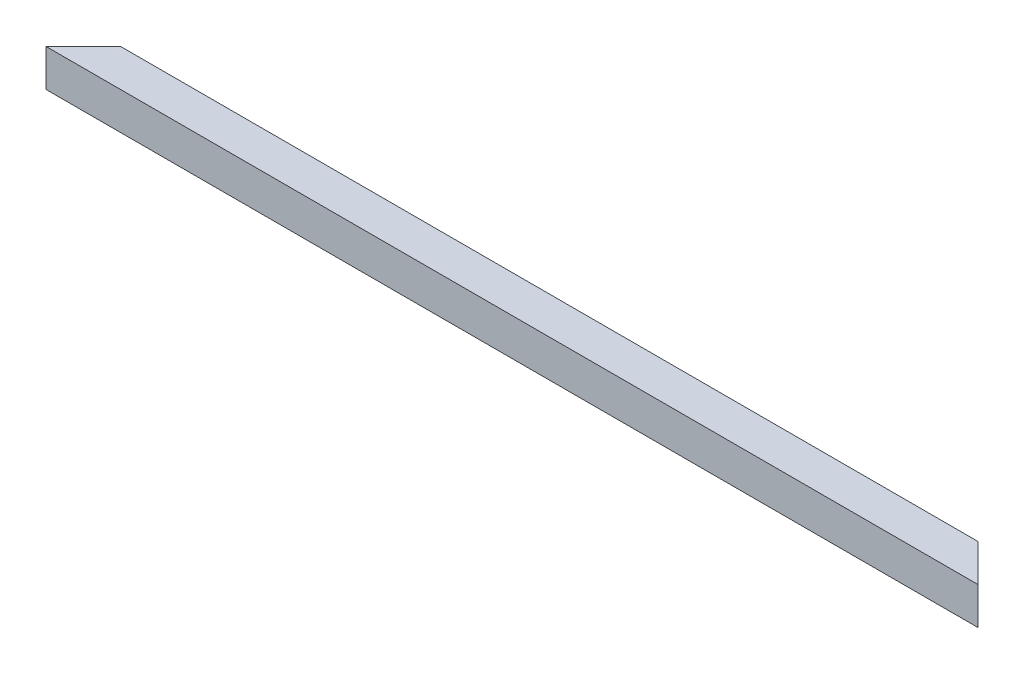
SolidWorks part; units mm, degrees
ref_plane "Alzado" through (0, 0, 0) normal (0, 0, 1) x (1, 0, 0)
ref_plane "Planta" through (0, 0, 0) normal (0, 1, 0) x (1, 0, 0)
ref_plane "Vista lateral" through (0, 0, 0) normal (1, 0, 0) x (0, 0, -1)
sketch "Croquis1" plane through (0, 0, 0) normal (1, 0, 0) x (0, 0, -1)
  line L1 (-20, -20) -> (20, -20)
  line L2 (-20, -20) -> (-20, 20)
  line L3 (-20, 20) -> (20, 20)
  line L4 (20, -20) -> (20, 20)
  line L5 (-20, -20) -> (20, 20) construction
  line L6 (-20, 20) -> (20, -20) construction
  line L7 (18, -18) -> (-18, -18)
  line L8 (18, -18) -> (18, 18)
  line L9 (18, 18) -> (-18, 18)
  line L10 (-18, -18) -> (-18, 18)
  line L11 (18, -18) -> (-18, 18) construction
  line L12 (18, 18) -> (-18, -18) construction
  point P0 (0, 0)
  point P6 (0, 0)
  dimension "D1" = 40
  dimension "D2" = 40
  dimension "D3" = 2
  dimension "D4" = 2
extrude "Saliente-Extruir1" add sketch "Croquis1" along normal blind 1000
sketch "Croquis2" plane through (0, 20, 0) normal (0, 1, 0) x (1, 0, 0)
  line L0 (0, -20) -> (40, 20)
  line L1 (1000, 20) -> (0, 20) construction
  line L2 (40, 20) -> (0, 20)
  line L3 (0, 20) -> (0, -20) construction
  line L4 (0, 20) -> (0, -20)
  line L5 (500, -20) -> (500, -75.3193) construction
  line L6 (1000, -20) -> (0, -20) construction
  line L7 (1000, 20) -> (1000, -20)
  line L8 (960, 20) -> (1000, 20)
  line L9 (1000, -20) -> (960, 20)
  dimension "D1" = 40
extrude "Cortar-Extruir1" cut sketch "Croquis2" against normal through all
